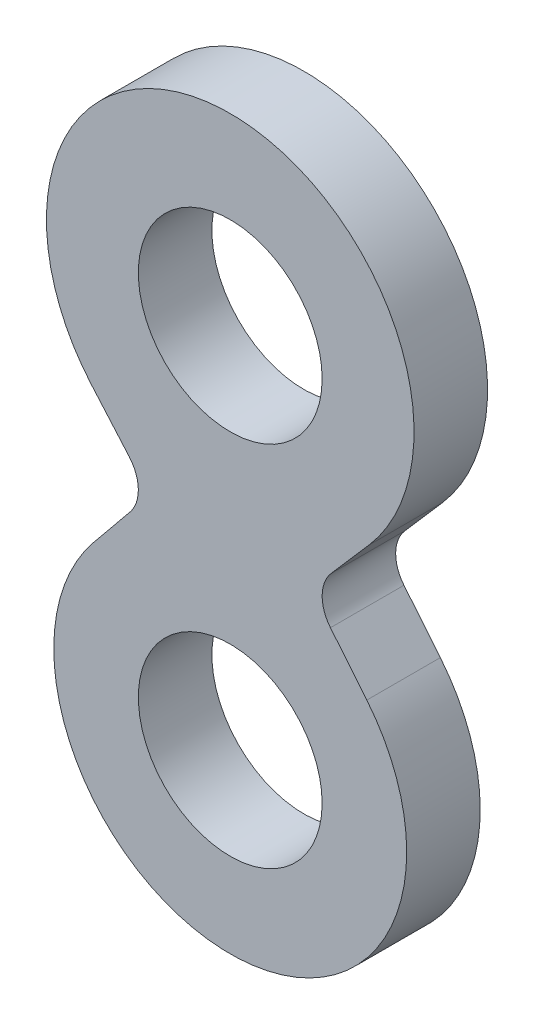
SolidWorks part; units mm, degrees
material "6061-T6 (SS)"
ref_plane "Front Plane" through (0, 0, 0) normal (0, 0, 1) x (1, 0, 0)
ref_plane "Top Plane" through (0, 0, 0) normal (0, 1, 0) x (1, 0, 0)
ref_plane "Right Plane" through (0, 0, 0) normal (1, 0, 0) x (0, 0, -1)
sketch "Sketch1" plane through (0, 0, 0) normal (0, 0, 1) x (1, 0, 0)
  line L2 (17.4347, 35.1691) -> (23.9513, 42.6578)
  line L3 (17.3096, 26.9806) -> (23.5941, 19.2963)
  line L4 (-23.5941, 19.2963) -> (-17.3096, 26.9806)
  line L5 (-17.4347, 35.1691) -> (-23.9513, 42.6578)
  arc A0 (-23.5941, 19.2963) -> (23.5941, 19.2963) centre (0, 0) ccw
  arc A1 (23.9513, 42.6578) -> (-23.9513, 42.6578) centre (0, 63.5) ccw
  circle A2 centre (0, 63.5) radius 15.875
  circle A3 centre (0, 0) radius 15.875
  arc A4 (-17.3096, 26.9806) -> (-17.4347, 35.1691) centre (-22.225, 31.0007) ccw
  arc A5 (17.4347, 35.1691) -> (17.3096, 26.9806) centre (22.225, 31.0007) ccw
  point P15 (-20.4416, 34.3654)
  point P16 (-26.4691, 25.3962)
  point P17 (-24.6236, 50.6822)
  point P18 (-20.1159, 19.7712)
  point P19 (0, 0)
  point P20 (-17.6181, 29.0428)
  point P21 (-18.6621, 35.1493)
  point P22 (12.6646, 54.1032)
  point P23 (9.934, 14.4818)
  point P24 (12.0251, 16.1787)
  point P25 (-16.8611, 47.2991)
  point P26 (-27.6157, 58.0541)
  point P27 (-12.1986, 31.3054)
  point P28 (-28.3615, 36.3926)
  point P29 (-4.4583, 69.85)
  point P30 (18.4783, 54.5157)
  point P31 (0, 0)
  point P32 (15.9905, 19.9313)
  point P33 (32.8591, 33.3836)
  point P34 (21.8664, 12.7343)
  point P35 (21.4329, 13.3951)
  point P36 (18.6432, 17.2508)
  point P37 (16.2761, 19.5)
  point P38 (12.2711, 23.4061)
  point P39 (17.5295, 18.4323)
  point P40 (0, 0)
  point P41 (27.1108, 34.4943)
  point P42 (0, 0)
  point P43 (18.1363, 17.783)
  point P44 (12.9664, 22.6409)
  point P45 (18.6509, 17.2425)
  point P46 (15.8194, 49.601)
  point P47 (17.484, 51.4253)
  point P48 (19.0766, 16.7703)
  point P49 (0, 0)
  point P50 (17.0889, 18.7918)
  point P51 (56.1954, 33.6077)
  point P52 (23.6947, 7.6867)
  point P53 (22.5909, 11.6685)
  point P54 (15.1106, 24.1388)
  point P55 (15.1329, 37.7331)
  point P56 (21.4884, 13.5428)
  point P57 (17.4238, 46.1774)
  point P58 (21.4884, 58.6572)
  point P59 (23.8084, 9.7559)
  point P60 (0, 0)
  point P61 (19.5687, 25.4)
  point P62 (0, 0)
  point P63 (-22.225, 28.575)
  dimension "D1" = 30.48
  dimension "D3" = 31.75
  dimension "D4" = 31.75
  dimension "D5" = 44.45
  dimension "D6" = 6.35
  dimension "D7" = 31.75
  dimension "D2" = 63.5
extrude "Boss-Extrude1" add sketch "Sketch1" along normal blind 12.7
ref_point "Point1"
